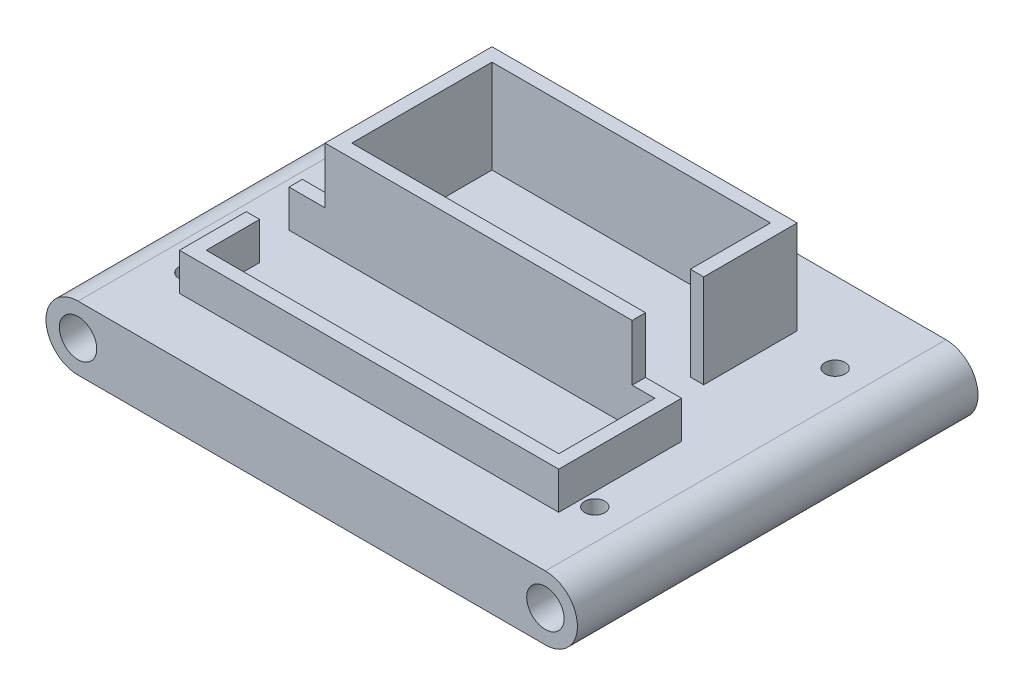
SolidWorks part; units mm, degrees
ref_plane "Front Plane" through (0, 0, 0) normal (0, 0, 1) x (1, 0, 0)
ref_plane "Top Plane" through (0, 0, 0) normal (0, 1, 0) x (1, 0, 0)
ref_plane "Right Plane" through (0, 0, 0) normal (1, 0, 0) x (0, 0, -1)
sketch "Sketch1" plane through (0, 0, 0) normal (0, 0, 1) x (1, 0, 0)
  line L0 (0, -55) -> (0, 55) construction
  line L1 (-44.45, 6.096) -> (44.45, 6.096)
  line L2 (-44.45, -6.096) -> (44.45, -6.096)
  arc A0 (44.45, -6.096) -> (44.45, 6.096) centre (44.45, 0) ccw
  arc A1 (-44.45, -6.096) -> (-44.45, 6.096) centre (-44.45, 0) cw
  circle A2 centre (-44.45, 0) radius 3.556
  circle A3 centre (44.45, 0) radius 3.556
extrude "Boss-Extrude1" add sketch "Sketch1" along normal blind 76.2
sketch "Sketch2" plane through (0, -6.096, 0) normal (0, -1, 0) x (1, 0, 0)
  circle A0 centre (-9.144, 69.215) radius 1.905
  circle A1 centre (27.051, 60.833) radius 1.905
  circle A2 centre (-28.956, 69.215) radius 1.905
  circle A3 centre (-28.956, 6.985) radius 1.905
  circle A4 centre (-9.144, 6.985) radius 1.905
  circle A5 centre (11.049, 60.833) radius 1.905
  circle A6 centre (11.049, 15.367) radius 1.905
  circle A7 centre (27.051, 15.367) radius 1.905
  dimension "D1" = 2
  dimension "D2" = 2
  dimension "D3" = 2
  dimension "D4" = 2
extrude "Cut-Extrude1" cut sketch "Sketch2" against normal blind 6.604
sketch "Sketch3" plane through (0, 6.096, 0) normal (0, 1, 0) x (1, 0, 0)
  line L1 (-29.21, -15.24) -> (28.8477, -15.24)
  line L2 (-29.21, -15.24) -> (-29.21, -12.7)
  line L3 (-29.21, -12.7) -> (28.8477, -12.7)
  line L4 (28.8477, -15.24) -> (28.8477, -12.7)
  line L5 (-29.21, -44.45) -> (29.21, -44.45)
  line L6 (-29.21, -44.45) -> (-29.21, -41.91)
  line L7 (-29.21, -41.91) -> (29.21, -41.91)
  line L8 (29.21, -44.45) -> (29.21, -41.91)
  line L9 (-29.21, -41.91) -> (-26.67, -41.91)
  line L10 (-29.21, -41.91) -> (-29.21, -15.24)
  line L11 (-29.21, -15.24) -> (-26.67, -15.24)
  line L12 (-26.67, -41.91) -> (-26.67, -15.24)
  line L17 (28.8477, -15.24) -> (26.3077, -15.24)
  line L18 (28.8477, -15.24) -> (28.8477, -30.48)
  line L19 (28.8477, -30.48) -> (26.3077, -30.48)
  line L20 (26.3077, -15.24) -> (26.3077, -30.48)
  point P0 (0, 0)
  point P1 (0, 0)
  dimension "D1" = 2.54
  dimension "D2" = 2.54
  dimension "D3" = 58.42
  dimension "D4" = 2.54
  dimension "D5" = 2.54
  dimension "D6" = 15.24
extrude "Boss-Extrude2" add sketch "Sketch3" along normal blind 17.78 contours L1 L4 L3 L2 | L7 L12 L1 L10 | L5 L8 L7 L6 | L18 L19 L20 L17
sketch "Sketch4" plane through (0, 6.096, 0) normal (0, 1, 0) x (1, 0, 0)
  line L1 (29.21, -44.45) -> (36.068, -44.45)
  line L2 (29.21, -44.45) -> (29.21, -41.91)
  line L3 (29.21, -41.91) -> (36.068, -41.91)
  line L4 (36.068, -44.45) -> (36.068, -41.91)
  line L5 (-29.21, -44.45) -> (-36.068, -44.45)
  line L6 (-29.21, -44.45) -> (-29.21, -41.91)
  line L7 (-29.21, -41.91) -> (-36.068, -41.91)
  line L8 (-36.068, -44.45) -> (-36.068, -41.91)
  line L13 (36.068, -44.45) -> (33.528, -44.45)
  line L14 (36.068, -44.45) -> (36.068, -62.738)
  line L15 (36.068, -62.738) -> (33.528, -62.738)
  line L16 (33.528, -44.45) -> (33.528, -62.738)
  line L17 (-36.068, -62.738) -> (36.068, -62.738)
  line L18 (-36.068, -62.738) -> (-36.068, -65.278)
  line L19 (-36.068, -65.278) -> (36.068, -65.278)
  line L20 (36.068, -62.738) -> (36.068, -65.278)
  line L21 (-36.068, -62.738) -> (-33.528, -62.738)
  line L22 (-36.068, -62.738) -> (-36.068, -52.578)
  line L23 (-36.068, -52.578) -> (-33.528, -52.578)
  line L24 (-33.528, -62.738) -> (-33.528, -52.578)
  line M19 (-29.21, -44.45) -> (-29.21, -12.7)
  line M27 (29.21, -41.91) -> (29.21, -44.45)
  dimension "D1" = 6.858
  dimension "D2" = 6.858
  dimension "D3" = 10.16
  dimension "D5" = 18.288
  dimension "D6" = 2.54
  dimension "D7" = 2.54
extrude "Boss-Extrude3" add sketch "Sketch4" along normal blind 7.112 contours L8 L5 L7 M19 | L17 L24 L23 L22 | L20 L15 L17 L18 L19 | L1 L16 L15 L14 | L1 L4 L3 M27
sketch "Sketch5" plane through (0, 6.096, 0) normal (0, 1, 0) x (1, 0, 0)
  circle A0 centre (38.608, -60.96) radius 1.905
  circle A1 centre (-38.608, -60.96) radius 1.905
  circle A2 centre (-38.608, -15.24) radius 1.905
  circle A3 centre (38.608, -15.24) radius 1.905
  dimension "D1" = 2
  dimension "D2" = 2
extrude "Cut-Extrude2" cut sketch "Sketch5" against normal blind 7.112
